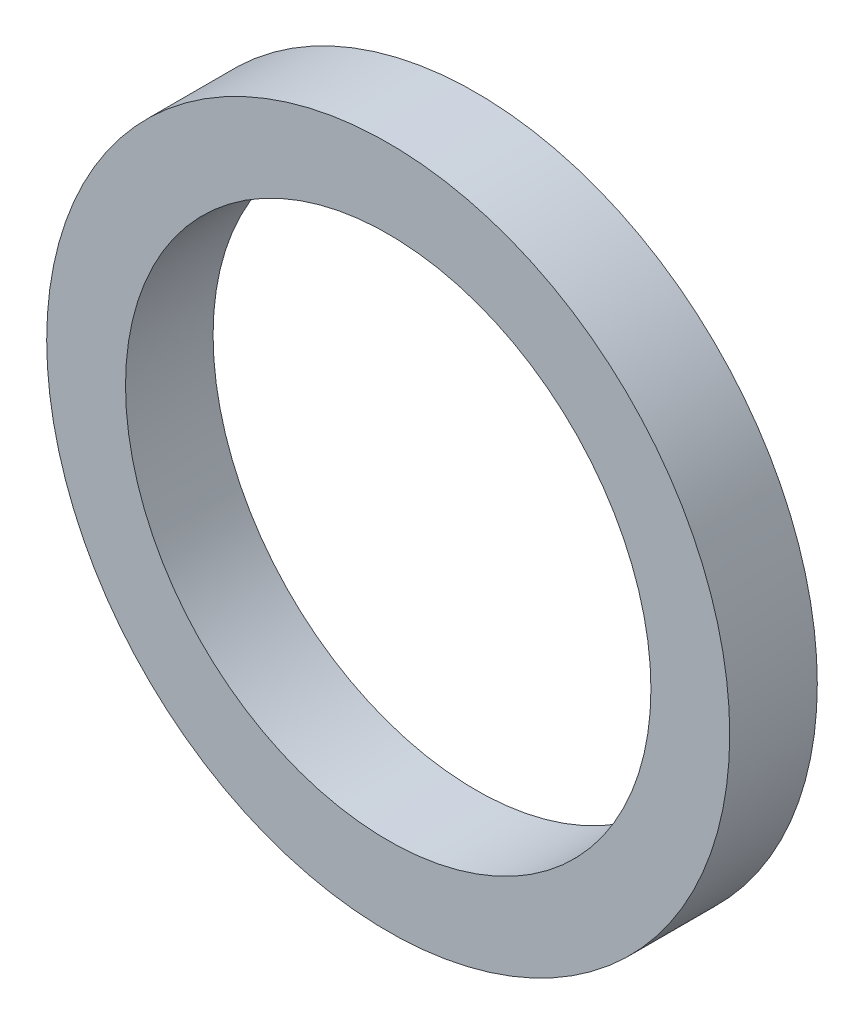
SolidWorks part; units mm, degrees
ref_plane "Front Plane" through (0, 0, 0) normal (0, 0, 1) x (1, 0, 0)
ref_plane "Top Plane" through (0, 0, 0) normal (0, 1, 0) x (1, 0, 0)
ref_plane "Right Plane" through (0, 0, 0) normal (1, 0, 0) x (0, 0, -1)
sketch "Sketch1" plane through (0, 0, 0) normal (0, 0, 1) x (1, 0, 0)
  circle A0 centre (0, 0) radius 30
  circle A1 centre (0, 0) radius 39
  dimension "D1" = 60
  dimension "D2" = 78
extrude "Boss-Extrude1" add sketch "Sketch1" along normal blind 10
